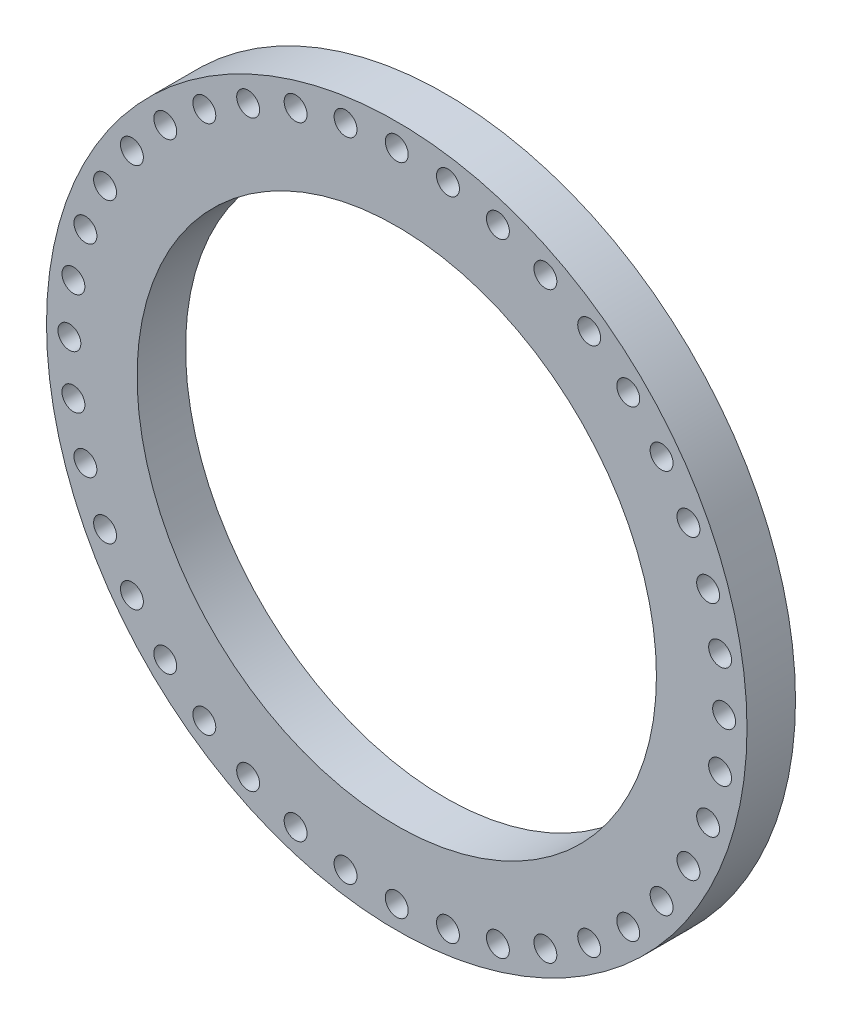
SolidWorks part; units mm, degrees
ref_plane "Front Plane" through (0, 0, 0) normal (0, 0, 1) x (1, 0, 0)
ref_plane "Top Plane" through (0, 0, 0) normal (0, 1, 0) x (1, 0, 0)
ref_plane "Right Plane" through (0, 0, 0) normal (1, 0, 0) x (0, 0, -1)
sketch "Sketch1" plane through (0, 0, 0) normal (0, 0, 1) x (1, 0, 0)
  circle A0 centre (0, 0) radius 24.095
  circle A1 centre (0, 0) radius 32.5
  circle A2 centre (0, 30.375) radius 1.0625
  circle A3 centre (4.7517, 30.001) radius 1.0625
  circle A4 centre (9.3864, 28.8883) radius 1.0625
  circle A5 centre (13.79, 27.0643) radius 1.0625
  circle A6 centre (17.854, 24.5739) radius 1.0625
  circle A7 centre (21.4784, 21.4784) radius 1.0625
  circle A8 centre (24.5739, 17.854) radius 1.0625
  circle A9 centre (27.0643, 13.79) radius 1.0625
  circle A10 centre (28.8883, 9.3864) radius 1.0625
  circle A11 centre (30.001, 4.7517) radius 1.0625
  circle A12 centre (30.375, 0) radius 1.0625
  circle A13 centre (30.001, -4.7517) radius 1.0625
  circle A14 centre (28.8883, -9.3864) radius 1.0625
  circle A15 centre (27.0643, -13.79) radius 1.0625
  circle A16 centre (24.5739, -17.854) radius 1.0625
  circle A17 centre (21.4784, -21.4784) radius 1.0625
  circle A18 centre (17.854, -24.5739) radius 1.0625
  circle A19 centre (13.79, -27.0643) radius 1.0625
  circle A20 centre (9.3864, -28.8883) radius 1.0625
  circle A21 centre (4.7517, -30.001) radius 1.0625
  circle A22 centre (0, -30.375) radius 1.0625
  circle A23 centre (-4.7517, -30.001) radius 1.0625
  circle A24 centre (-9.3864, -28.8883) radius 1.0625
  circle A25 centre (-13.79, -27.0643) radius 1.0625
  circle A26 centre (-17.854, -24.5739) radius 1.0625
  circle A27 centre (-21.4784, -21.4784) radius 1.0625
  circle A28 centre (-24.5739, -17.854) radius 1.0625
  circle A29 centre (-27.0643, -13.79) radius 1.0625
  circle A30 centre (-28.8883, -9.3864) radius 1.0625
  circle A31 centre (-30.001, -4.7517) radius 1.0625
  circle A32 centre (-30.375, 0) radius 1.0625
  circle A33 centre (-30.001, 4.7517) radius 1.0625
  circle A34 centre (-28.8883, 9.3864) radius 1.0625
  circle A35 centre (-27.0643, 13.79) radius 1.0625
  circle A36 centre (-24.5739, 17.854) radius 1.0625
  circle A37 centre (-21.4784, 21.4784) radius 1.0625
  circle A38 centre (-17.854, 24.5739) radius 1.0625
  circle A39 centre (-13.79, 27.0643) radius 1.0625
  circle A40 centre (-9.3864, 28.8883) radius 1.0625
  circle A41 centre (-4.7517, 30.001) radius 1.0625
  point P86 (0, 0)
  dimension "D1" = 40
  dimension "D2" = 2.125
  dimension "D3" = 21.4784
  dimension "D15" = 48.19
  dimension "D16" = 65
extrude "Boss-Extrude1" add sketch "Sketch1" along normal blind 4.5
scale "Scale1" scale about centroid uniform scaling yes scale factor 25.4
